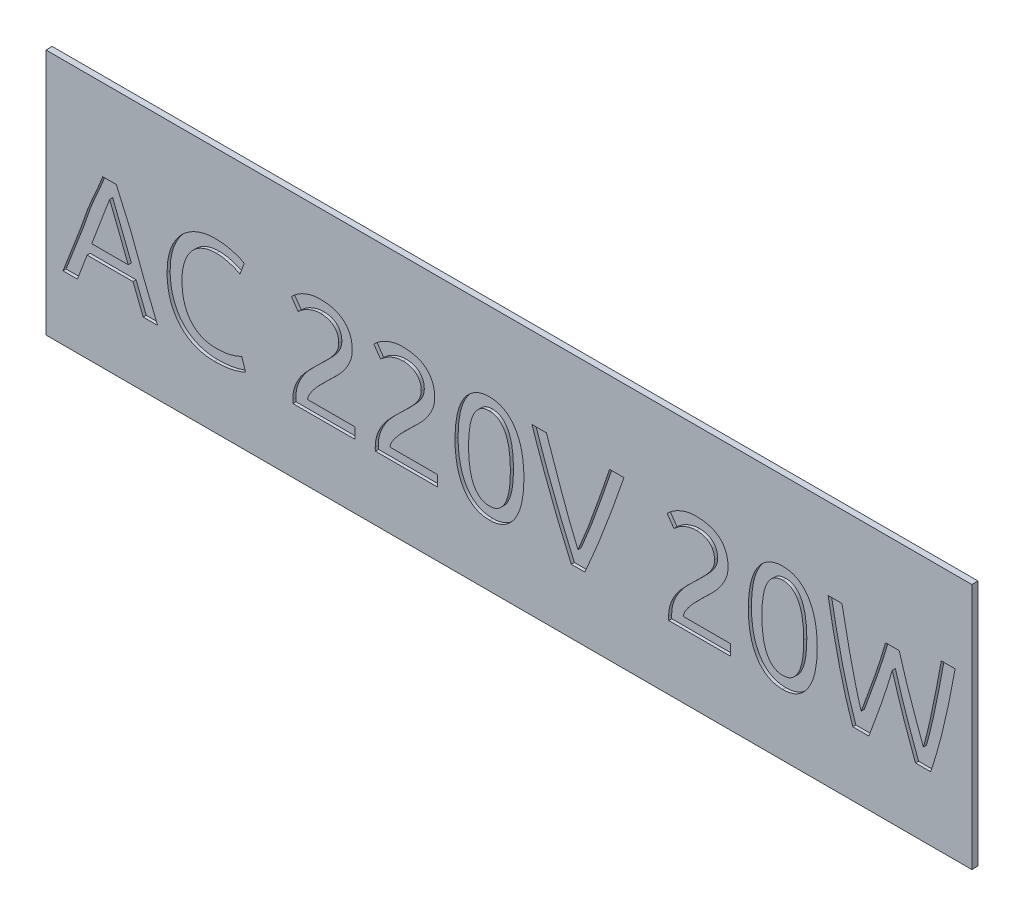
SolidWorks part; units mm, degrees
ref_plane "Front Plane" through (0, 0, 0) normal (0, 0, 1) x (1, 0, 0)
ref_plane "Top Plane" through (0, 0, 0) normal (0, 1, 0) x (1, 0, 0)
ref_plane "Right Plane" through (0, 0, 0) normal (1, 0, 0) x (0, 0, -1)
sketch "Sketch1" plane through (0, 0, 0) normal (0, 0, 1) x (1, 0, 0)
  line L1 (15, -4) -> (-15, -4)
  line L2 (15, -4) -> (15, 4)
  line L3 (15, 4) -> (-15, 4)
  line L4 (-15, -4) -> (-15, 4)
  line L5 (15, -4) -> (-15, 4) construction
  line L6 (15, 4) -> (-15, -4) construction
  point P0 (0, 0)
  dimension "D1" = 8
  dimension "D2" = 30
extrude "Boss-Extrude1" add sketch "Sketch1" along normal mid plane 0.2
sketch "Sketch2" plane through (0, 0, 0.1) normal (0, 0, 1) x (1, 0, 0)
  text T0 "AC 220V 20W" font "Ubuntu" height in points 12
extrude "Cut-Extrude1" cut sketch "Sketch2" against normal blind 0.1
